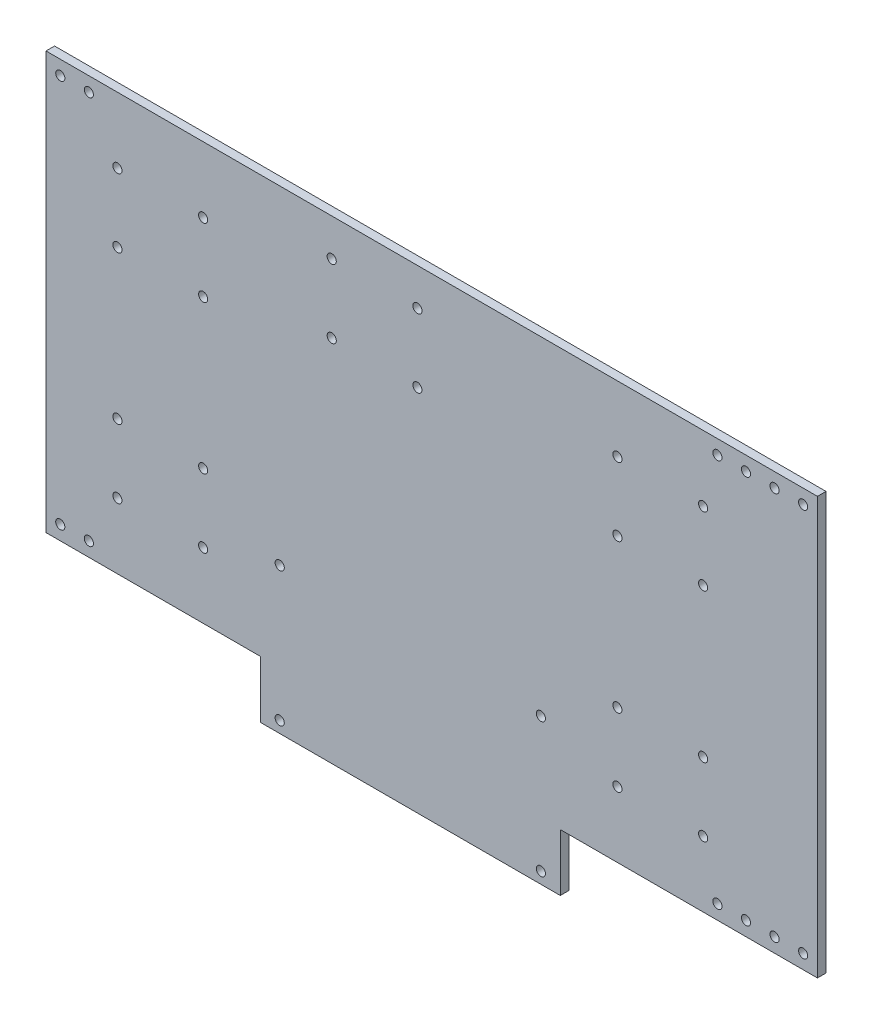
SolidWorks part; units mm, degrees
material "Thornel Mat VMA"
ref_plane "前视基准面" through (0, 0, 0) normal (0, 0, 1) x (1, 0, 0)
ref_plane "上视基准面" through (0, 0, 0) normal (0, 1, 0) x (1, 0, 0)
ref_plane "右视基准面" through (0, 0, 0) normal (1, 0, 0) x (0, 0, -1)
other "Configuration Table"
sketch "草图1" plane through (0, 0, 0) normal (0, 0, 1) x (1, 0, 0)
  line L0 (165.8789, -46.1294) -> (185.8789, -46.1294)
  line L1 (-59.1211, 0.8706) -> (-29.1211, 0.8706) construction
  line L2 (-59.1211, 0.8706) -> (-59.1211, -23.1294) construction
  line L3 (-59.1211, -23.1294) -> (-29.1211, -23.1294) construction
  line L4 (-29.1211, 0.8706) -> (-29.1211, -23.1294) construction
  line L5 (-64.1211, 8.8706) -> (-24.1211, 8.8706) construction
  line L6 (-64.1211, 8.8706) -> (-64.1211, -32.1294) construction
  line L7 (-64.1211, -32.1294) -> (-24.1211, -32.1294) construction
  line L8 (-24.1211, 8.8706) -> (-24.1211, -32.1294) construction
  line L9 (185.8789, -41.1294) -> (146.9644, -41.1294) construction
  line L10 (-79.1211, -46.1294) -> (-9.1211, -46.1294)
  line L13 (-9.1211, -46.1294) -> (-9.1211, -66.1294)
  line L14 (115.8789, 0.8706) -> (145.8789, 0.8706) construction
  line L15 (115.8789, 0.8706) -> (115.8789, -23.1294) construction
  line L16 (115.8789, -23.1294) -> (145.8789, -23.1294) construction
  line L17 (145.8789, 0.8706) -> (145.8789, -23.1294) construction
  line L18 (110.8789, 8.8706) -> (150.8789, 8.8706) construction
  line L19 (110.8789, 8.8706) -> (110.8789, -32.1294) construction
  line L20 (110.8789, -32.1294) -> (150.8789, -32.1294) construction
  line L21 (150.8789, 8.8706) -> (150.8789, -32.1294) construction
  line L22 (95.8789, -46.1294) -> (165.8789, -46.1294)
  line L23 (95.8789, -46.1294) -> (95.8789, -66.1294)
  line L26 (-9.1211, -46.1294) -> (95.8789, -46.1294) construction
  line L27 (-84.1211, 26.8706) -> (185.8789, 26.8706) construction
  line L30 (185.8789, 99.8706) -> (185.8789, -46.1294)
  line L31 (-2.3211, -15.1294) -> (89.0789, -15.1294) construction
  line L32 (-2.3211, -15.1294) -> (-2.3211, -62.1294) construction
  line L33 (-2.3211, -62.1294) -> (89.0789, -62.1294) construction
  line L34 (89.0789, -15.1294) -> (89.0789, -62.1294) construction
  line L35 (-9.1211, -66.1294) -> (95.8789, -66.1294)
  line L41 (-9.1211, 99.8706) -> (95.8789, 99.8706)
  line L42 (150.8789, 44.8706) -> (150.8789, 85.8706) construction
  line L43 (110.8789, 85.8706) -> (150.8789, 85.8706) construction
  line L44 (110.8789, 44.8706) -> (110.8789, 85.8706) construction
  line L45 (110.8789, 44.8706) -> (150.8789, 44.8706) construction
  line L46 (145.8789, 52.8706) -> (145.8789, 76.8706) construction
  line L47 (115.8789, 76.8706) -> (145.8789, 76.8706) construction
  line L48 (115.8789, 52.8706) -> (115.8789, 76.8706) construction
  line L49 (115.8789, 52.8706) -> (145.8789, 52.8706) construction
  line L50 (146.9644, -41.1294) -> (146.9644, -46.1294) construction
  line L51 (-24.1211, 44.8706) -> (-24.1211, 85.8706) construction
  line L52 (-64.1211, 85.8706) -> (-24.1211, 85.8706) construction
  line L53 (-64.1211, 44.8706) -> (-64.1211, 85.8706) construction
  line L54 (-64.1211, 44.8706) -> (-24.1211, 44.8706) construction
  line L55 (-29.1211, 52.8706) -> (-29.1211, 76.8706) construction
  line L56 (-59.1211, 76.8706) -> (-29.1211, 76.8706) construction
  line L57 (-59.1211, 52.8706) -> (-59.1211, 76.8706) construction
  line L58 (-59.1211, 52.8706) -> (-29.1211, 52.8706) construction
  line L59 (165.8789, 99.8706) -> (185.8789, 99.8706)
  line L65 (95.8789, 99.8706) -> (165.8789, 99.8706)
  line L68 (-79.1211, 99.8706) -> (-9.1211, 99.8706)
  line L69 (43.3789, 99.8706) -> (43.3789, -15.1294) construction
  line L78 (30.8789, 94.8706) -> (30.8789, 53.8706) construction
  line L79 (15.8789, 86.8706) -> (45.8789, 86.8706) construction
  line L80 (15.8789, 86.8706) -> (15.8789, 62.8706) construction
  line L81 (15.8789, 62.8706) -> (45.8789, 62.8706) construction
  line L82 (45.8789, 86.8706) -> (45.8789, 62.8706) construction
  line L83 (10.8789, 94.8706) -> (50.8789, 94.8706) construction
  line L84 (10.8789, 94.8706) -> (10.8789, 53.8706) construction
  line L85 (50.8789, 94.8706) -> (50.8789, 53.8706) construction
  line L86 (50.8789, 53.8706) -> (10.8789, 53.8706) construction
  line L87 (-79.1211, -46.1294) -> (-79.1211, 99.8706) construction
  line L88 (-79.1211, 99.8706) -> (-84.1211, 99.8706)
  line L90 (-84.1211, -46.1294) -> (-79.1211, -46.1294)
  line L91 (165.8789, -46.1294) -> (165.8789, 99.8706) construction
  line L92 (-9.1211, 99.8706) -> (-9.1211, 26.8706) construction
  line L93 (95.8789, 99.8706) -> (95.8789, 26.8706) construction
  line L94 (-84.1211, -46.1294) -> (-84.1211, 99.8706)
  line L95 (-79.1211, -41.1294) -> (-69.1211, -41.1294) construction
  circle A0 centre (-59.1211, 0.8706) radius 1.6
  circle A1 centre (-29.1211, 0.8706) radius 1.6
  circle A2 centre (-59.1211, -23.1294) radius 1.6
  circle A3 centre (-29.1211, -23.1294) radius 1.6
  circle A4 centre (115.8789, 0.8706) radius 1.6
  circle A5 centre (145.8789, 0.8706) radius 1.6
  circle A6 centre (115.8789, -23.1294) radius 1.6
  circle A7 centre (145.8789, -23.1294) radius 1.6
  circle A8 centre (-2.3211, -62.1294) radius 1.6
  circle A9 centre (-2.3211, -15.1294) radius 1.6
  circle A10 centre (89.0789, -15.1294) radius 1.6
  circle A11 centre (89.0789, -62.1294) radius 1.6
  circle A16 centre (145.8789, 76.8706) radius 1.6
  circle A17 centre (115.8789, 76.8706) radius 1.6
  circle A18 centre (145.8789, 52.8706) radius 1.6
  circle A19 centre (115.8789, 52.8706) radius 1.6
  circle A20 centre (-29.1211, 76.8706) radius 1.6
  circle A21 centre (-59.1211, 76.8706) radius 1.6
  circle A22 centre (-29.1211, 52.8706) radius 1.6
  circle A23 centre (-59.1211, 52.8706) radius 1.6
  circle A36 centre (15.8789, 86.8706) radius 1.6
  circle A37 centre (45.8789, 86.8706) radius 1.6
  circle A38 centre (15.8789, 62.8706) radius 1.6
  circle A39 centre (45.8789, 62.8706) radius 1.6
  circle A40 centre (-79.1211, -41.1294) radius 1.6
  circle A41 centre (-69.1211, -41.1294) radius 1.6
  circle A42 centre (-79.1211, 94.8706) radius 1.6
  circle A43 centre (-69.1211, 94.8706) radius 1.6
  circle A44 centre (180.8789, -41.1294) radius 1.6
  circle A45 centre (170.8789, -41.1294) radius 1.6
  circle A46 centre (160.8789, -41.1294) radius 1.6
  circle A47 centre (150.8789, -41.1294) radius 1.6
  circle A48 centre (180.8789, 94.8706) radius 1.6
  circle A49 centre (170.8789, 94.8706) radius 1.6
  circle A50 centre (160.8789, 94.8706) radius 1.6
  circle A51 centre (150.8789, 94.8706) radius 1.6
  point P12 (-44.1211, 8.8706)
  point P13 (-44.1211, 0.8706)
  point P33 (130.8789, 8.8706)
  point P34 (130.8789, 0.8706)
  point P54 (43.3789, -62.1294)
  point P55 (43.3789, -46.1294)
  point P80 (-44.1211, -23.1294)
  point P81 (-44.1211, -46.1294)
  point P82 (130.8789, -23.1294)
  point P83 (130.8789, -46.1294)
  point P153 (30.8789, 94.8706)
  point P154 (30.8789, 86.8706)
  dimension "D3" = 3.2
  dimension "D13" = 3.2
  dimension "D22" = 3.2
  dimension "D29" = 270
  dimension "D41" = 3.2
  dimension "D37" = 3.2
  dimension "D17" = 5
  dimension "D27" = 3.2
  dimension "D31" = 10
  dimension "D1" = 30
  dimension "D2" = 24
  dimension "D4" = 40
  dimension "D5" = 41
  dimension "D6" = 8
  dimension "D7" = 16
  dimension "D8" = 4
  dimension "D9" = 5
  dimension "D10" = 14
  dimension "D11" = 30
  dimension "D12" = 24
  dimension "D14" = 40
  dimension "D15" = 41
  dimension "D16" = 8
  dimension "D18" = 20
  dimension "D19" = 10
  dimension "D20" = 14
  dimension "D21" = 105
  dimension "D23" = 20
  dimension "D24" = 91.4
  dimension "D25" = 47
  dimension "D26" = 5
  dimension "D28" = 146
  dimension "D30" = 5
  dimension "D32" = 5
  dimension "D33" = 14
  dimension "D34" = 14
  dimension "D35" = 10
  dimension "D36" = 10
  dimension "D39" = 30
  dimension "D40" = 24
  dimension "D42" = 40
  dimension "D43" = 41
  dimension "D44" = 8
extrude "凸台-拉伸1" add sketch "草图1" along normal blind 3
